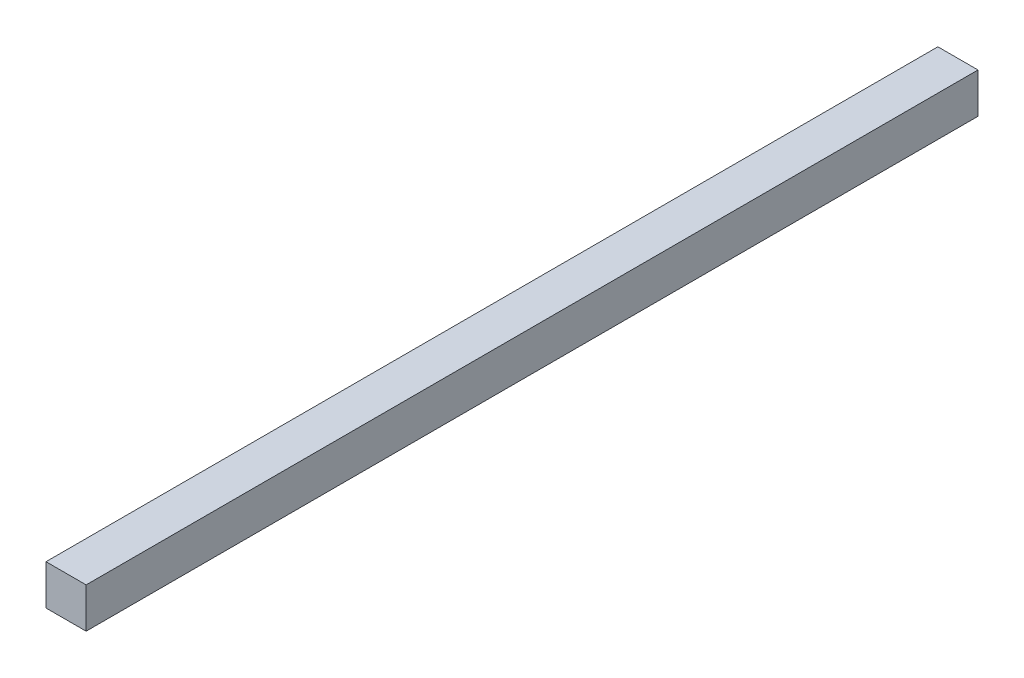
SolidWorks part; units mm, degrees
ref_plane "Face" through (0, 0, 0) normal (0, 0, 1) x (1, 0, 0)
ref_plane "Dessus" through (0, 0, 0) normal (0, 1, 0) x (1, 0, 0)
ref_plane "Droite" through (0, 0, 0) normal (1, 0, 0) x (0, 0, -1)
sketch "Esquisse1" plane through (0, 0, 0) normal (0, 0, 1) x (1, 0, 0)
  line L1 (0, 0) -> (18, 0)
  line L2 (0, 0) -> (0, 18)
  line L3 (0, 18) -> (18, 18)
  line L4 (18, 0) -> (18, 18)
  dimension "D1" = 18
  dimension "D2" = 18
extrude "Extrusion1" add sketch "Esquisse1" against normal blind 400
